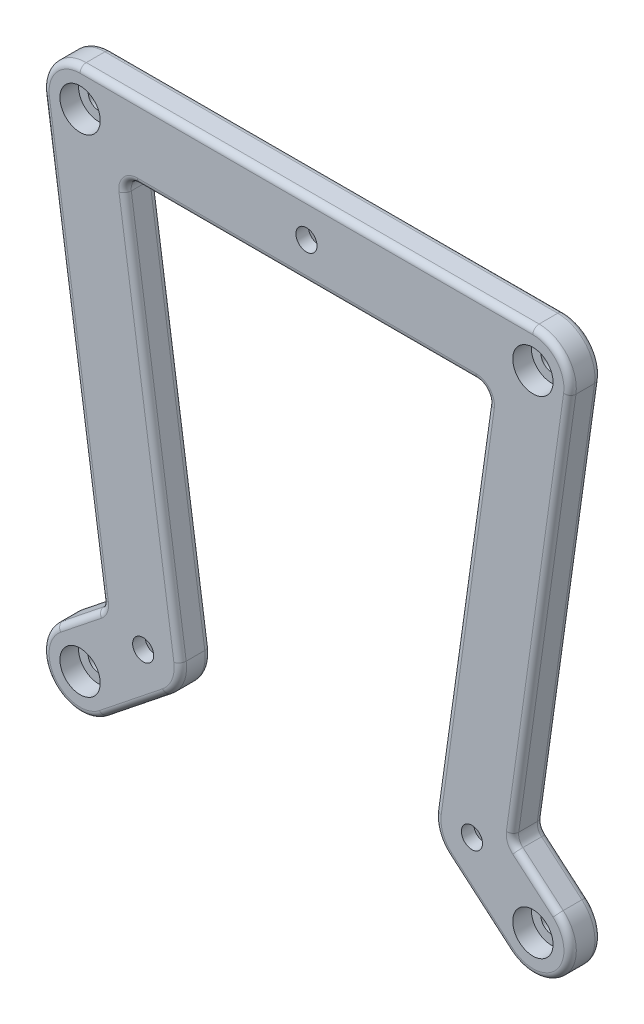
SolidWorks part; units mm, degrees
ref_plane "Plan de face" through (0, 0, 0) normal (0, 0, 1) x (1, 0, 0)
ref_plane "Plan de dessus" through (0, 0, 0) normal (0, 1, 0) x (1, 0, 0)
ref_plane "Plan de droite" through (0, 0, 0) normal (1, 0, 0) x (0, 0, -1)
sketch "Esquisse1" plane through (0, 0, 0) normal (0, 0, 1) x (1, 0, 0)
  line L0 (0, 35.05) -> (0, -35.05) construction
  line L1 (26.67, -35.05) -> (-26.33, -35.05) construction
  line L2 (-26.33, -35.05) -> (-26.33, -35.33) construction
  line L3 (36.5, 35.05) -> (-36.5, 35.05) construction
  line L4 (36.5, -43.45) -> (-36.5, -43.45) construction
  line L5 (36.5, 35.05) -> (36.5, -43.45) construction
  line L6 (-22.5863, -40.0188) -> (-32.7563, -48.1388)
  line L7 (22.7721, -39.6114) -> (32.6021, -48.0114)
  line L8 (42.4419, 34.2168) -> (32.6119, -35.8832) construction
  line L9 (30.5679, -30.4886) -> (40.3979, -38.8886) construction
  line L10 (33.0687, -32.6256) -> (40.3979, -38.8886)
  line L11 (33.0687, -32.6256) -> (42.4419, 34.2168)
  line L12 (36.5, 41.05) -> (-36.5, 41.05)
  line L13 (-36.5, 29.05) -> (36.5, 29.05) construction
  line L14 (30.5581, 35.8832) -> (20.7281, -34.2168) construction
  line L15 (-30.5617, 35.9081) -> (-20.3917, -34.4719) construction
  line L16 (-20.3917, -34.4719) -> (-29.5707, 29.05)
  line L17 (-29.5707, 29.05) -> (29.5999, 29.05)
  line L18 (29.5999, 29.05) -> (20.7281, -34.2168)
  line L19 (-42.4383, 34.1919) -> (-32.2683, -36.1881) construction
  line L20 (-40.2437, -38.7612) -> (-30.0737, -30.6412) construction
  line L21 (-40.2437, -38.7612) -> (-32.7599, -32.786)
  line L22 (-32.7599, -32.786) -> (-42.4383, 34.1919)
  circle A0 centre (0, 35.05) radius 1.7
  circle A1 centre (-26.33, -35.33) radius 1.7
  circle A2 centre (26.67, -35.05) radius 1.7
  circle A3 centre (0, 35.05) radius 6 construction
  circle A4 centre (-26.33, -35.33) radius 6 construction
  circle A5 centre (26.67, -35.05) radius 6 construction
  circle A6 centre (-36.5, 35.05) radius 1.7
  circle A7 centre (36.5, 35.05) radius 1.7
  circle A8 centre (-36.5, 35.05) radius 6 construction
  circle A9 centre (36.5, 35.05) radius 6 construction
  circle A10 centre (-36.5, -43.45) radius 1.7
  circle A11 centre (36.5, -43.45) radius 1.7
  circle A12 centre (-36.5, -43.45) radius 6 construction
  circle A13 centre (36.5, -43.45) radius 6 construction
  arc A14 (40.3979, -38.8886) -> (32.6021, -48.0114) centre (36.5, -43.45) cw
  arc A15 (20.7281, -34.2168) -> (22.7721, -39.6114) centre (26.67, -35.05) ccw
  arc A16 (-20.3917, -34.4719) -> (-22.5863, -40.0188) centre (-26.33, -35.33) cw
  arc A17 (-36.5, 41.05) -> (-42.4383, 34.1919) centre (-36.5, 35.05) ccw
  arc A18 (42.4419, 34.2168) -> (36.5, 41.05) centre (36.5, 35.05) ccw
  arc A19 (-40.2437, -38.7612) -> (-32.7563, -48.1388) centre (-36.5, -43.45) ccw
  point P0 (0, 0)
  point P29 (0, 35.05)
  dimension "D1" = 3.4
  dimension "D2" = 12
  dimension "D8" = 3.4
  dimension "D9" = 12
  dimension "D11" = 3.4
  dimension "D12" = 12
  dimension "D3" = 0.28
  dimension "D4" = 53
  dimension "D5" = 70.1
  dimension "D6" = 26.67
  dimension "D7" = 73
  dimension "D10" = 73
  dimension "D13" = 78.5
extrude "Boss.-Extru.1" add sketch "Esquisse1" along normal blind 5
fillet "Congé1" radius 2 4 edges at (-29.5707, 29.05, 2.5) (29.5999, 29.05, 2.5) (33.0687, -32.6256, 2.5) (-32.7599, -32.786, 2.5)
sketch "Esquisse2" plane through (0, 0, 5) normal (0, 0, 1) x (1, 0, 0)
  circle A0 centre (-36.5, 35.05) radius 3.25
  circle A1 centre (36.5, 35.05) radius 3.25
  circle A2 centre (36.5, -43.45) radius 3.25
  circle A3 centre (-36.5, -43.45) radius 3.25
  dimension "D1" = 6.5
extrude "Enlèv. mat.-Extru.1" cut sketch "Esquisse2" against normal offset from surface (3 mm away) 2 up to face at (-34.8, -43.45, 0)
sketch "Esquisse3" plane through (0, 0, 0) normal (0, 0, -1) x (-1, 0, 0)
  line L0 (-1.6454, 37.9) -> (1.6454, 37.9)
  line L1 (1.6454, 37.9) -> (3.2909, 35.05)
  line L2 (3.2909, 35.05) -> (1.6454, 32.2)
  line L3 (1.6454, 32.2) -> (-1.6454, 32.2)
  line L4 (-1.6454, 32.2) -> (-3.2909, 35.05)
  line L5 (-3.2909, 35.05) -> (-1.6454, 37.9)
  line L6 (-3.2909, 35.05) -> (3.2909, 35.05) construction
  line L7 (-28.3154, -32.2) -> (-25.0246, -32.2)
  line L8 (-25.0246, -32.2) -> (-23.3791, -35.05)
  line L9 (-23.3791, -35.05) -> (-25.0246, -37.9)
  line L10 (-25.0246, -37.9) -> (-28.3154, -37.9)
  line L11 (-28.3154, -37.9) -> (-29.9609, -35.05)
  line L12 (-29.9609, -35.05) -> (-28.3154, -32.2)
  line L13 (-29.9609, -35.05) -> (-23.3791, -35.05) construction
  line L14 (24.6846, -32.48) -> (27.9754, -32.48)
  line L15 (27.9754, -32.48) -> (29.6209, -35.33)
  line L16 (29.6209, -35.33) -> (27.9754, -38.18)
  line L17 (27.9754, -38.18) -> (24.6846, -38.18)
  line L18 (24.6846, -38.18) -> (23.0391, -35.33)
  line L19 (23.0391, -35.33) -> (24.6846, -32.48)
  line L20 (23.0391, -35.33) -> (29.6209, -35.33) construction
  point P2 (-26.67, -35.05)
  point P7 (26.33, -35.33)
  point P20 (0, 35.05)
  point P21 (0, 35.05)
  point P25 (-26.67, -35.05)
  point P26 (3.2909, 35.05)
  point P27 (-24.2547, -39.2334)
  point P28 (26.33, -35.33)
  point P29 (-25.0246, -37.9)
  dimension "D1" = 120
  dimension "D2" = 5.7
  dimension "D3" = 120
  dimension "D4" = 120
  dimension "D5" = 5.7
  dimension "D6" = 5.7
extrude "Enlèv. mat.-Extru.2" cut sketch "Esquisse3" against normal offset from surface (3 mm away) 2 up to face at (-33.25, -43.45, 5)
fillet "Congé2" radius 1 40 edges at (-41.0359, 38.9776, 0) (0, 41.05, 0) (41.0277, 38.987, 0) (37.8314, 1.3385, 0) (33.3313, -32.5261, 0) (37.1501, -36.1132, 0) (41.0614, -47.3479, 0) (27.6871, -43.8114, 0) (21.0592, -37.1759, 0) (25.0043, -3.7223, 0) (28.8091, 28.3623, 0) (0.0195, 29.05, 0) (-28.7729, 28.3592, 0) (-24.816, -3.854, 0) (-20.7508, -37.5374, 0) (-27.6713, -44.0788, 0) (-41.1888, -47.1937, 0) (-36.9495, -36.131, 0) (-33.0435, -32.6738, 0) (33.3313, -32.5261, 5) (37.1501, -36.1132, 5) (41.0614, -47.3479, 5) (27.6871, -43.8114, 5) (21.0592, -37.1759, 5) (25.0043, -3.7223, 5) (28.8091, 28.3623, 5) (0.0195, 29.05, 5) (-28.7729, 28.3592, 5) (-24.816, -3.854, 5) (-20.7508, -37.5374, 5) (-27.6713, -44.0788, 5) (-41.1888, -47.1937, 5) (-36.9495, -36.131, 5) (-33.0435, -32.6738, 5) (-37.6811, 1.27, 5) (-41.0359, 38.9776, 5) (0, 41.05, 5) (41.0277, 38.987, 5) (-37.6811, 1.27, 0) (37.8314, 1.3385, 5)
